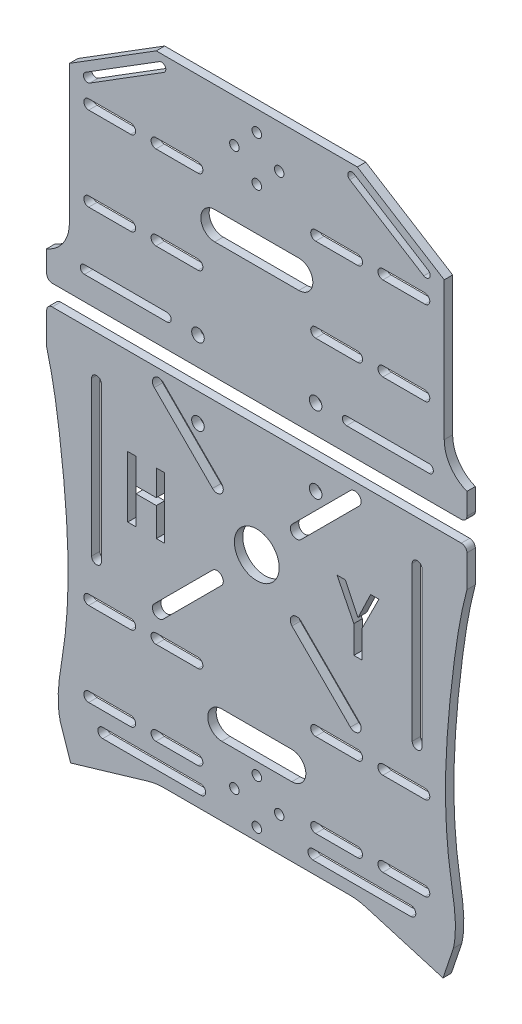
SolidWorks part; units mm, degrees
ref_plane "前视基准面" through (0, 0, 0) normal (0, 0, 1) x (1, 0, 0)
ref_plane "上视基准面" through (0, 0, 0) normal (0, 1, 0) x (1, 0, 0)
ref_plane "右视基准面" through (0, 0, 0) normal (1, 0, 0) x (0, 0, -1)
sketch "草图1" plane through (0, 0, 0) normal (0, 0, 1) x (1, 0, 0)
  line L0 (0, 148.5) -> (0, -94.9538) construction
  line L1 (105, -148.5) -> (-105, -148.5) construction
  line L2 (105, -148.5) -> (105, 148.5) construction
  line L3 (105, 148.5) -> (-105, 148.5) construction
  line L4 (-105, -148.5) -> (-105, 148.5) construction
  line L5 (105, -148.5) -> (-105, 148.5) construction
  line L6 (105, 148.5) -> (-105, -148.5) construction
  line L7 (35.8892, 121.6645) -> (-35.8892, 121.6645)
  line L8 (-35.8892, 121.6645) -> (-66.9017, 102.292)
  line L9 (-75, 40.9339) -> (-75, 31.2613)
  line L10 (-66.9017, 102.292) -> (-66.9017, 52.8701)
  line L11 (75, 40.9339) -> (75, 31.2613)
  line L12 (66.9017, 102.292) -> (66.9017, 52.8701)
  line L13 (35.8892, 121.6645) -> (66.9017, 102.292)
  line L14 (-75, 31.2613) -> (75, 31.2613)
  line L15 (-60, -148.5) -> (-60, -91.8129)
  line L16 (-75, 23.94) -> (75, 23.94)
  line L17 (-75, 23.94) -> (-75, 10.5626)
  line L18 (-38.8455, -105.5906) -> (-66.4608, -113.7617)
  line L19 (-66.4608, -113.7617) -> (-70.1743, -102.7328)
  line L20 (75, 23.94) -> (75, 10.5626)
  line L21 (66.4608, -113.7617) -> (70.1743, -102.7328)
  line L22 (38.8455, -105.5906) -> (66.4608, -113.7617)
  line L23 (-105, 93.0519) -> (105, 93.0519)
  line L24 (-105, 63.0519) -> (105, 63.0519)
  line L25 (-105, -90.0629) -> (-70.5337, -90.0629)
  line L26 (-105, -60.0629) -> (-67.4027, -60.0629)
  line L27 (60, -148.5) -> (60, 148.5)
  line L28 (-60, -58.3129) -> (-45, -58.3129)
  line L29 (-60, -61.8129) -> (-45, -61.8129)
  line L30 (-36, -58.3129) -> (-21, -58.3129)
  line L31 (-36, -61.8129) -> (-21, -61.8129)
  line L32 (-60, -88.3129) -> (-45, -88.3129)
  line L33 (-60, -91.8129) -> (-45, -91.8129)
  line L34 (-36, -88.3129) -> (-21, -88.3129)
  line L35 (-36, -91.8129) -> (-21, -91.8129)
  line L36 (-60, -58.3129) -> (-60, 148.5)
  line L37 (-19.25, -90.0629) -> (105, -90.0629)
  line L38 (-19.25, -60.0629) -> (19.25, -60.0629)
  line L39 (-60, -88.3129) -> (-60, -61.8129)
  line L40 (21, -58.3129) -> (36, -58.3129)
  line L41 (45, -58.3129) -> (60, -58.3129)
  line L42 (60, -61.8129) -> (45, -61.8129)
  line L43 (36, -61.8129) -> (21, -61.8129)
  line L44 (21, -88.3129) -> (36, -88.3129)
  line L45 (21, -91.8129) -> (36, -91.8129)
  line L46 (45, -88.3129) -> (60, -88.3129)
  line L47 (45, -91.8129) -> (60, -91.8129)
  line L48 (37.75, -60.0629) -> (43.25, -60.0629)
  line L49 (58.25, -60.0629) -> (105, -60.0629)
  line L50 (-60, 94.8019) -> (-45, 94.8019)
  line L51 (-36, 94.8019) -> (-21, 94.8019)
  line L52 (-60, 91.3019) -> (-45, 91.3019)
  line L53 (-36, 91.3019) -> (-21, 91.3019)
  line L54 (-60, 64.8019) -> (-45, 64.8019)
  line L55 (-60, 61.3019) -> (-45, 61.3019)
  line L56 (-36, 64.8019) -> (-21, 64.8019)
  line L57 (-36, 61.3019) -> (-21, 61.3019)
  line L58 (21, 94.8019) -> (36, 94.8019)
  line L59 (21, 91.3019) -> (36, 91.3019)
  line L60 (45, 94.8019) -> (60, 94.8019)
  line L61 (45, 91.3019) -> (60, 91.3019)
  line L62 (21, 61.3019) -> (36, 61.3019)
  line L63 (21, 64.8019) -> (36, 64.8019)
  line L64 (45, 61.3019) -> (60, 61.3019)
  line L65 (45, 64.8019) -> (60, 64.8019)
  line L66 (-33.1709, -104.7687) -> (33.1709, -104.7687)
  line L67 (0, -104.7687) -> (0, -148.5) construction
  arc A0 (-75, 40.9339) -> (-66.9017, 52.8701) centre (-79.7474, 52.8701) ccw
  arc A1 (75, 40.9339) -> (66.9017, 52.8701) centre (79.7474, 52.8701) cw
  arc A3 (-60, -88.3129) -> (-60, -91.8129) centre (-60, -90.0629) ccw
  arc A4 (-60, -58.3129) -> (-60, -61.8129) centre (-60, -60.0629) ccw
  circle A5 centre (-60, 63.0519) radius 1.75
  circle A6 centre (-60, 93.0519) radius 1.75
  circle A7 centre (60, 93.0519) radius 1.75
  circle A8 centre (60, 63.0519) radius 1.75
  arc A9 (60, -91.8129) -> (60, -88.3129) centre (60, -90.0629) ccw
  arc A10 (60, -61.8129) -> (60, -58.3129) centre (60, -60.0629) ccw
  arc A11 (-36, -58.3129) -> (-36, -61.8129) centre (-36, -60.0629) ccw
  arc A12 (-36, -88.3129) -> (-36, -91.8129) centre (-36, -90.0629) ccw
  arc A13 (36, -61.8129) -> (36, -58.3129) centre (36, -60.0629) ccw
  arc A14 (36, -91.8129) -> (36, -88.3129) centre (36, -90.0629) ccw
  arc A15 (-45, -61.8129) -> (-45, -58.3129) centre (-45, -60.0629) ccw
  arc A16 (-21, -61.8129) -> (-21, -58.3129) centre (-21, -60.0629) ccw
  arc A17 (-45, -91.8129) -> (-45, -88.3129) centre (-45, -90.0629) ccw
  arc A18 (-21, -91.8129) -> (-21, -88.3129) centre (-21, -90.0629) ccw
  arc A19 (45, -58.3129) -> (45, -61.8129) centre (45, -60.0629) ccw
  arc A20 (21, -58.3129) -> (21, -61.8129) centre (21, -60.0629) ccw
  arc A21 (21, -88.3129) -> (21, -91.8129) centre (21, -90.0629) ccw
  arc A22 (45, -88.3129) -> (45, -91.8129) centre (45, -90.0629) ccw
  circle A23 centre (-36, 93.0519) radius 1.75
  circle A24 centre (-36, 63.0519) radius 1.75
  circle A25 centre (36, 93.0519) radius 1.75
  circle A26 centre (36, 63.0519) radius 1.75
  circle A27 centre (-45, 93.0519) radius 1.75
  circle A28 centre (-21, 93.0519) radius 1.75
  circle A29 centre (-45, 63.0519) radius 1.75
  circle A30 centre (-21, 63.0519) radius 1.75
  circle A31 centre (21, 93.0519) radius 1.75
  circle A32 centre (21, 63.0519) radius 1.75
  circle A33 centre (45, 93.0519) radius 1.75
  circle A34 centre (45, 63.0519) radius 1.75
  arc A35 (33.1709, -104.7687) -> (38.8455, -105.5906) centre (33.1709, -124.7687) cw
  arc A36 (-33.1709, -104.7687) -> (-38.8455, -105.5906) centre (-33.1709, -124.7687) ccw
  spline S0 degree 3 poles (-75, 10.5626) (-72.6959, 1.9073) (-70.3396, -13.3728) (-67.1028, -43.6255) (-66.7657, -72.9327) (-71.8903, -95.1489) (-70.1743, -102.7328) knots 0 0 0 0 0.235247 0.406294 0.801186 1 1 1 1
  spline S1 degree 3 poles (75, 10.5626) (72.6959, 1.9073) (70.3396, -13.3728) (67.1028, -43.6255) (66.7657, -72.9327) (71.8903, -95.1489) (70.1743, -102.7328) knots 0 0 0 0 0.235247 0.406294 0.801186 1 1 1 1
  point P0 (0, 0)
  point P27 (0, 121.6645)
  point P42 (0, -94.0966)
  dimension "D1" = 60
  dimension "D4" = 20
  dimension "D5" = 24
  dimension "D7" = 24
  dimension "D9" = 15
  dimension "D10" = 15
  dimension "D13" = 24
  dimension "D17" = 15
  dimension "D2" = 30
  dimension "D3" = 30
  dimension "D6" = 24
  dimension "D8" = 24
  dimension "D11" = 15
  dimension "D12" = 15
  dimension "D14" = 24
  dimension "D15" = 24
  dimension "D16" = 24
  dimension "D18" = 15
  dimension "D19" = 15
  dimension "D20" = 15
  dimension "D21" = 15
  dimension "D22" = 15
  dimension "D23" = 15
  dimension "D24" = 15
  dimension "D25" = 15
  dimension "D26" = 15
  dimension "D27" = 15
  dimension "D28" = 15
  dimension "D29" = 3.5
  dimension "D30" = 3.5
  dimension "D31" = 3.5
extrude "凸台-拉伸1" add sketch "草图1" along normal blind 3
sketch "草图7" plane through (0, 0, 0) normal (0, 0, -1) x (-1, 0, 0)
  line L0 (0, 121.6645) -> (0, -104.7687) construction
  line L1 (-35.8892, 121.6645) -> (35.8892, 121.6645) construction
  line L2 (33.1709, -104.7687) -> (-33.1709, -104.7687) construction
  line L3 (0, 41.2613) -> (-21, 41.2613) construction
  line L4 (0, 41.2613) -> (21, 41.2613) construction
  line L5 (0, 13.94) -> (-21, 13.94) construction
  line L6 (0, 13.94) -> (21, 13.94) construction
  line L7 (75, 23.94) -> (-75, 23.94) construction
  line L8 (75, 31.2613) -> (-75, 31.2613) construction
  circle A0 centre (-21, 41.2613) radius 2.25
  circle A1 centre (21, 41.2613) radius 2.25
  circle A2 centre (-21, 13.94) radius 2.25
  circle A3 centre (21, 13.94) radius 2.25
  dimension "D1" = 10
  dimension "D2" = 10
extrude "切除-拉伸2" cut sketch "草图7" against normal through all
sketch "草图8" plane through (0, 0, 3) normal (0, 0, 1) x (1, 0, 0)
  line L0 (0, 121.6645) -> (0, -1.9696) construction
  line L1 (35.8892, 121.6645) -> (-35.8892, 121.6645) construction
  line L2 (-33.1709, -104.7687) -> (33.1709, -104.7687) construction
  line L3 (-33.409, 20.409) -> (-12.6214, -0.3786)
  line L4 (31.818, -51.182) -> (-31.818, -51.182)
  line L5 (35, -48) -> (35, 15.6418)
  line L8 (-35, 18.818) -> (-12.6214, -3.5605) construction
  line L9 (-33.409, -52.773) -> (-12.5737, -31.9377)
  line L10 (-36.591, 17.227) -> (-15.8034, -3.5605)
  line L11 (33.4105, 20.4105) -> (12.573, -0.427)
  line L12 (15.803, -3.5609) -> (36.5881, 17.2241)
  line L13 (31.8195, 18.8195) -> (-31.818, 18.818)
  line L14 (-15.8038, -28.8038) -> (-36.591, -49.591)
  line L15 (12.5534, -31.9174) -> (33.409, -52.773)
  line L16 (34.9993, 18.8173) -> (12.6207, -3.5613) construction
  line L17 (0, -30.3951) -> (0, -104.7687) construction
  line L18 (-35, -48) -> (-35, 15.636)
  line L19 (-11.9624, -1.9696) -> (-14.2124, -1.9696) construction
  line L20 (15.8034, -28.8034) -> (36.591, -49.591)
  line L21 (14.2117, -30.3951) -> (11.9607, -30.3951) construction
  line L22 (14.2117, -30.3951) -> (14.2117, -28.1441) construction
  line L23 (14.2117, -1.9696) -> (11.9612, -1.9696) construction
  line L24 (-14.2124, -30.3951) -> (-14.2124, -28.1446) construction
  line L25 (14.2117, -30.3951) -> (12.62, -28.8034) construction
  line L26 (14.2117, -1.9696) -> (12.6204, -3.5609) construction
  line L27 (12.6207, -28.8027) -> (35, -51.182) construction
  line L28 (-12.6215, -3.5606) -> (-14.2124, -1.9696) construction
  line L29 (-14.2124, -4.2196) -> (-14.2124, -1.9696) construction
  line L30 (-12.6214, -28.8034) -> (-35, -51.182) construction
  line L31 (-12.6211, -28.8037) -> (-14.2124, -30.3951) construction
  line L32 (-11.9619, -30.3951) -> (-14.2124, -30.3951) construction
  line L33 (14.2117, -4.2201) -> (14.2117, -1.9696) construction
  line L34 (11.0312, -30.3951) -> (0, -30.3951) construction
  arc A0 (-33.409, 20.409) -> (-36.591, 17.227) centre (-35, 18.818) ccw
  arc A1 (36.5881, 17.2241) -> (33.4105, 20.4105) centre (34.9993, 18.8173) ccw
  arc A2 (-36.591, -49.591) -> (-33.409, -52.773) centre (-35, -51.182) ccw
  arc A3 (33.409, -52.773) -> (36.591, -49.591) centre (35, -51.182) ccw
  arc A4 (-15.8034, -3.5605) -> (-12.6214, -0.3786) centre (-14.2124, -1.9696) ccw
  arc A5 (12.6692, -0.3308) -> (15.803, -3.5609) centre (14.2117, -1.9696) ccw
  arc A6 (-12.6699, -32.0338) -> (-15.8038, -28.8038) centre (-14.2124, -30.3951) ccw
  arc A7 (15.8034, -28.8034) -> (12.6894, -32.0534) centre (14.2117, -30.3951) ccw
  circle A8 centre (-0.0004, -16.1823) radius 8
  point P6 (0, -16.182)
  point P13 (-0.0004, -16.1823)
extrude "切除-拉伸3" cut sketch "草图8" against normal through all
sketch "草图9" plane through (0, 0, 3) normal (0, 0, 1) x (1, 0, 0)
  line L0 (-70.7828, -98.747) -> (70.7828, -98.747) construction
  line L1 (0, -98.747) -> (0, -104.7687) construction
  line L2 (55, -100.497) -> (20, -100.497)
  line L3 (-55, -96.997) -> (-20, -96.997)
  line L4 (-55, -100.497) -> (-20, -100.497)
  line L5 (-33.1709, -104.7687) -> (33.1709, -104.7687) construction
  line L6 (55, -96.997) -> (20, -96.997)
  arc A0 (-55, -96.997) -> (-55, -100.497) centre (-55, -98.747) ccw
  arc A1 (-20, -100.497) -> (-20, -96.997) centre (-20, -98.747) ccw
  arc A2 (20, -100.497) -> (20, -96.997) centre (20, -98.747) cw
  arc A3 (55, -96.997) -> (55, -100.497) centre (55, -98.747) cw
  spline S0 degree 3 poles (-75, 10.5626) (-72.6959, 1.9073) (-70.3396, -13.3728) (-67.1028, -43.6255) (-66.7657, -72.9327) (-71.8903, -95.1489) (-70.1743, -102.7328) knots 0 0 0 0 0.235247 0.406294 0.801186 1 1 1 1 construction
  spline S1 degree 3 poles (75, 10.5626) (72.6959, 1.9073) (70.3396, -13.3728) (67.1028, -43.6255) (66.7657, -72.9327) (71.8903, -95.1489) (70.1743, -102.7328) knots 0 0 0 0 0.235247 0.406294 0.801186 1 1 1 1 construction
  dimension "D1" = 35
  dimension "D2" = 20
extrude "切除-拉伸4" cut sketch "草图9" against normal blind 3
sketch "草图10" plane through (0, 0, 3) normal (0, 0, 1) x (1, 0, 0)
  line L0 (-21, -60.0629) -> (-21, -90.0629) construction
  line L1 (21, -60.0629) -> (21, -90.0629) construction
  line L2 (-21, -75.0629) -> (-17.5, -75.0629) construction
  line L4 (12.5, -80.0629) -> (-12.5, -80.0629)
  line L6 (12.5, -70.0629) -> (-12.5, -70.0629)
  line L11 (17.5, -75.0629) -> (21, -75.0629) construction
  arc A0 (-12.5, -70.0629) -> (-12.5, -80.0629) centre (-12.5, -75.0629) ccw
  arc A1 (12.5, -80.0629) -> (12.5, -70.0629) centre (12.5, -75.0629) ccw
  point P11 (0, -75.0629)
extrude "切除-拉伸5" cut sketch "草图10" against normal blind 3
sketch "草图11" plane through (0, 0, 3) normal (0, 0, 1) x (1, 0, 0)
  line L0 (-21, 93.0519) -> (-21, 63.0519) construction
  line L1 (21, 93.0519) -> (21, 63.0519) construction
  line L2 (-21, 78.0519) -> (-20, 78.0519) construction
  line L4 (15, 73.0519) -> (-15, 73.0519)
  line L6 (15, 83.0519) -> (-15, 83.0519)
  line L10 (20, 78.0519) -> (21, 78.0519) construction
  arc A0 (-15, 83.0519) -> (-15, 73.0519) centre (-15, 78.0519) ccw
  arc A1 (15, 73.0519) -> (15, 83.0519) centre (15, 78.0519) ccw
  point P10 (0, 78.0519)
  dimension "D1" = 30
extrude "切除-拉伸8" cut sketch "草图11" against normal blind 3
sketch "草图12" plane through (0, 0, 3) normal (0, 0, 1) x (1, 0, 0)
  line L0 (0, 121.6645) -> (0, 83.0519) construction
  line L1 (35.8892, 121.6645) -> (-35.8892, 121.6645) construction
  line L2 (15, 83.0519) -> (-15, 83.0519) construction
  circle A0 centre (0, 106.3718) radius 11 construction
  circle A1 centre (0, 106.3718) radius 8 construction
  circle A2 centre (0, 114.3718) radius 1.7
  circle A3 centre (0, 98.3718) radius 1.7
  circle A4 centre (8, 106.3718) radius 1.7
  circle A5 centre (-8, 106.3718) radius 1.7
extrude "切除-拉伸9" cut sketch "草图12" against normal blind 3
sketch "草图13" plane through (0, 0, 3) normal (0, 0, 1) x (1, 0, 0)
  line L0 (0, -104.7687) -> (0, -80.0629) construction
  line L1 (-33.1709, -104.7687) -> (33.1709, -104.7687) construction
  line L2 (-12.5, -80.0629) -> (12.5, -80.0629) construction
  circle A0 centre (0, -92.4158) radius 8 construction
  circle A1 centre (0, -84.4158) radius 1.7
  circle A2 centre (8, -92.4158) radius 1.7
  circle A3 centre (0, -100.4158) radius 1.7
  circle A4 centre (-8, -92.4158) radius 1.7
extrude "切除-拉伸11" cut sketch "草图13" against normal blind 3
sketch "草图14" plane through (0, 0, 3) normal (0, 0, 1) x (1, 0, 0)
  line L0 (0, 23.94) -> (0, -104.7687) construction
  line L1 (-55.4755, 8.9197) -> (-55.4755, -46.0803)
  line L2 (-58.9755, 8.9197) -> (-58.9755, -46.0803)
  line L3 (-75, 23.94) -> (75, 23.94) construction
  line L4 (-33.1709, -104.7687) -> (33.1709, -104.7687) construction
  line L5 (58.9755, 8.9197) -> (58.9755, -46.0803)
  line L6 (55.4755, 8.9197) -> (55.4755, -46.0803)
  arc A0 (-55.4755, 8.9197) -> (-58.9755, 8.9197) centre (-57.2255, 8.9197) ccw
  arc A1 (-58.9755, -46.0803) -> (-55.4755, -46.0803) centre (-57.2255, -46.0803) ccw
  arc A2 (58.9755, -46.0803) -> (55.4755, -46.0803) centre (57.2255, -46.0803) cw
  arc A3 (55.4755, 8.9197) -> (58.9755, 8.9197) centre (57.2255, 8.9197) cw
extrude "切除-拉伸12" cut sketch "草图14" against normal through all
fillet "圆角1" radius 2 2 edges at (75, 31.2613, 1.5) (-75, 31.2613, 1.5)
fillet "圆角2" radius 2 2 edges at (-75, 23.94, 1.5) (75, 23.94, 1.5)
sketch "草图15" plane through (0, 0, 0) normal (0, 0, -1) x (-1, 0, 0)
  line L0 (0, 121.6645) -> (0, 31.2613) construction
  line L1 (-35.8892, 121.6645) -> (35.8892, 121.6645) construction
  line L2 (73, 31.2613) -> (-73, 31.2613) construction
  line L3 (-27.5188, 121.6645) -> (-63.6963, 99.0657) construction
  line L4 (-35.8892, 121.6645) -> (-66.9017, 102.292) construction
  line L5 (-61.1842, 102.4035) -> (-34.7748, 118.9006)
  line L6 (-59.5948, 99.8591) -> (-33.1854, 116.3562)
  line L7 (27.5188, 121.6645) -> (63.6963, 99.0657) construction
  line L8 (59.5948, 99.8591) -> (33.1854, 116.3562)
  line L9 (61.1842, 102.4035) -> (34.7748, 118.9006)
  arc A0 (-61.1842, 102.4035) -> (-59.5948, 99.8591) centre (-60.3895, 101.1313) ccw
  arc A1 (-33.1854, 116.3562) -> (-34.7748, 118.9006) centre (-33.9801, 117.6284) ccw
  arc A2 (33.1854, 116.3562) -> (34.7748, 118.9006) centre (33.9801, 117.6284) cw
  arc A3 (61.1842, 102.4035) -> (59.5948, 99.8591) centre (60.3895, 101.1313) cw
extrude "切除-拉伸13" cut sketch "草图15" against normal through all
sketch "草图16" plane through (0, 0, 0) normal (0, 0, -1) x (-1, 0, 0)
  line L0 (0, 121.6645) -> (0, 31.2613) construction
  line L1 (-35.8892, 121.6645) -> (35.8892, 121.6645) construction
  line L2 (73, 31.2613) -> (-73, 31.2613) construction
  line L3 (-21, 41.2613) -> (-66.71, 41.2613) construction
  line L4 (-61.517, 42.7613) -> (-32.0563, 42.7613)
  line L5 (-61.517, 39.7613) -> (-32.0563, 39.7613)
  line L6 (21, 41.2613) -> (66.71, 41.2613) construction
  line L7 (61.517, 39.7613) -> (32.0563, 39.7613)
  line L8 (61.517, 42.7613) -> (32.0563, 42.7613)
  arc A0 (-61.517, 42.7613) -> (-61.517, 39.7613) centre (-61.517, 41.2613) ccw
  arc A1 (-32.0563, 39.7613) -> (-32.0563, 42.7613) centre (-32.0563, 41.2613) ccw
  arc A2 (32.0563, 39.7613) -> (32.0563, 42.7613) centre (32.0563, 41.2613) cw
  arc A3 (61.517, 42.7613) -> (61.517, 39.7613) centre (61.517, 41.2613) cw
extrude "切除-拉伸14" cut sketch "草图16" against normal through all
sketch "草图17" plane through (0, 0, 0) normal (0, 0, -1) x (-1, 0, 0)
  text T0 "Y" font "黑体" height in points 72
extrude "切除-拉伸15" cut sketch "草图17" against normal through all
sketch "草图18" plane through (0, 0, 0) normal (0, 0, -1) x (-1, 0, 0)
  text T0 "H" font "黑体" height in points 72
extrude "切除-拉伸16" cut sketch "草图18" against normal through all
